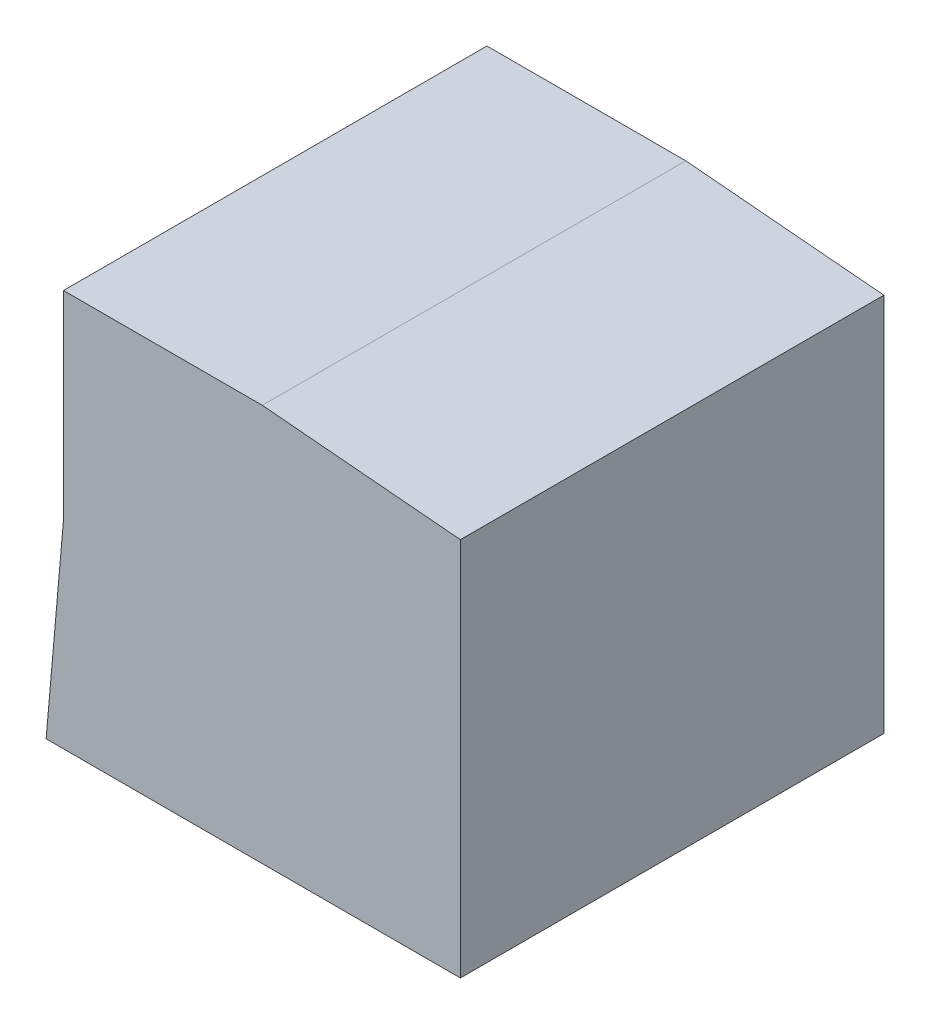
SolidWorks part; units mm, degrees
ref_plane "xy = von Vorne" through (0, 0, 0) normal (0, 0, 1) x (1, 0, 0)
ref_plane "zx = boden-parallel" through (0, 0, 0) normal (0, 1, 0) x (1, 0, 0)
ref_plane "yz = von Links" through (0, 0, 0) normal (1, 0, 0) x (0, 0, -1)
sketch "Skizze1" plane through (0, 0, 0) normal (0, 0, 1) x (1, 0, 0)
  line L0 (0, -18.7818) -> (-1.6369, -37.4922)
  line L1 (0, 0) -> (18.7818, 0)
  line L2 (0, 0) -> (0, -18.7818)
  line L3 (-1.6369, -37.4922) -> (37.4922, -37.4922)
  line L4 (37.4922, -1.6369) -> (37.4922, -37.4922)
  line L5 (18.7818, 0) -> (37.4922, -1.6369)
extrude "Aufsatz-Linear austragen1" add sketch "Skizze1" along normal blind 40
ref_plane "Ebene1" through (0, 5, 0) normal (0, 1, 0) x (1, 0, 0)
ref_plane "Ebene2" through (0.5784, 6.6117, 0) normal (0.0872, 0.9962, 0) x (0.9962, -0.0872, 0)
ref_plane "Ebene3" through (-5, 0, 0) normal (-1, 0, 0) x (0, 0, 1)
ref_plane "Ebene4" through (-3.3503, 0.2931, 0) normal (-0.9962, 0.0872, 0) x (0, 0, 1)
ref_plane "Ebene5" through (-3.3503, 0.2931, 0) normal (0.9962, -0.0872, 0) x (0, 0, -1)
equation "\"Angle\"= 5grad"
equation "\"D2@Skizze1\"= \"Angle\""
equation "\"D1@Skizze1\"= \"Angle\""
